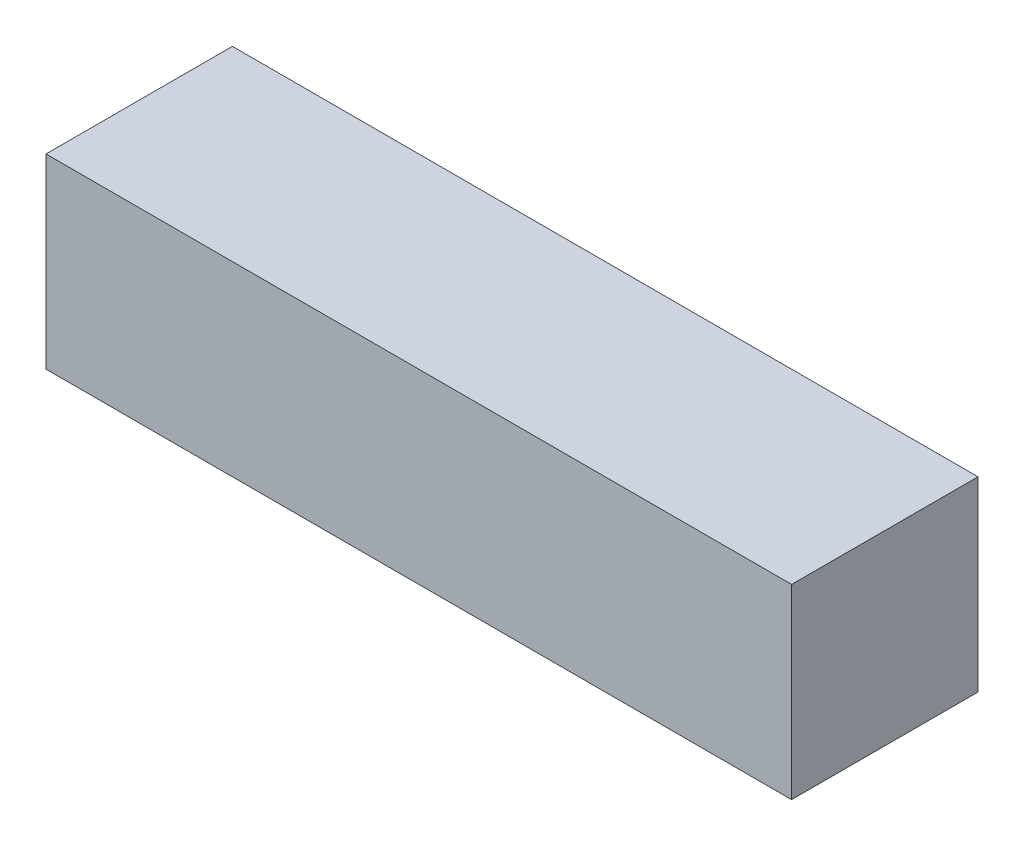
SolidWorks part; units mm, degrees
ref_plane "Front Plane" through (0, 0, 0) normal (0, 0, 1) x (1, 0, 0)
ref_plane "Top Plane" through (0, 0, 0) normal (0, 1, 0) x (1, 0, 0)
ref_plane "Right Plane" through (0, 0, 0) normal (1, 0, 0) x (0, 0, -1)
sketch "Sketch1" plane through (0, 0, 0) normal (0, 0, 1) x (1, 0, 0)
  line L1 (0, 0) -> (12.7, 0)
  line L2 (0, 0) -> (0, 3.175)
  line L3 (0, 3.175) -> (12.7, 3.175)
  line L4 (12.7, 0) -> (12.7, 3.175)
  dimension "D1" = 3.175
  dimension "D2" = 12.7
extrude "Boss-Extrude1" add sketch "Sketch1" along normal blind 3.175
